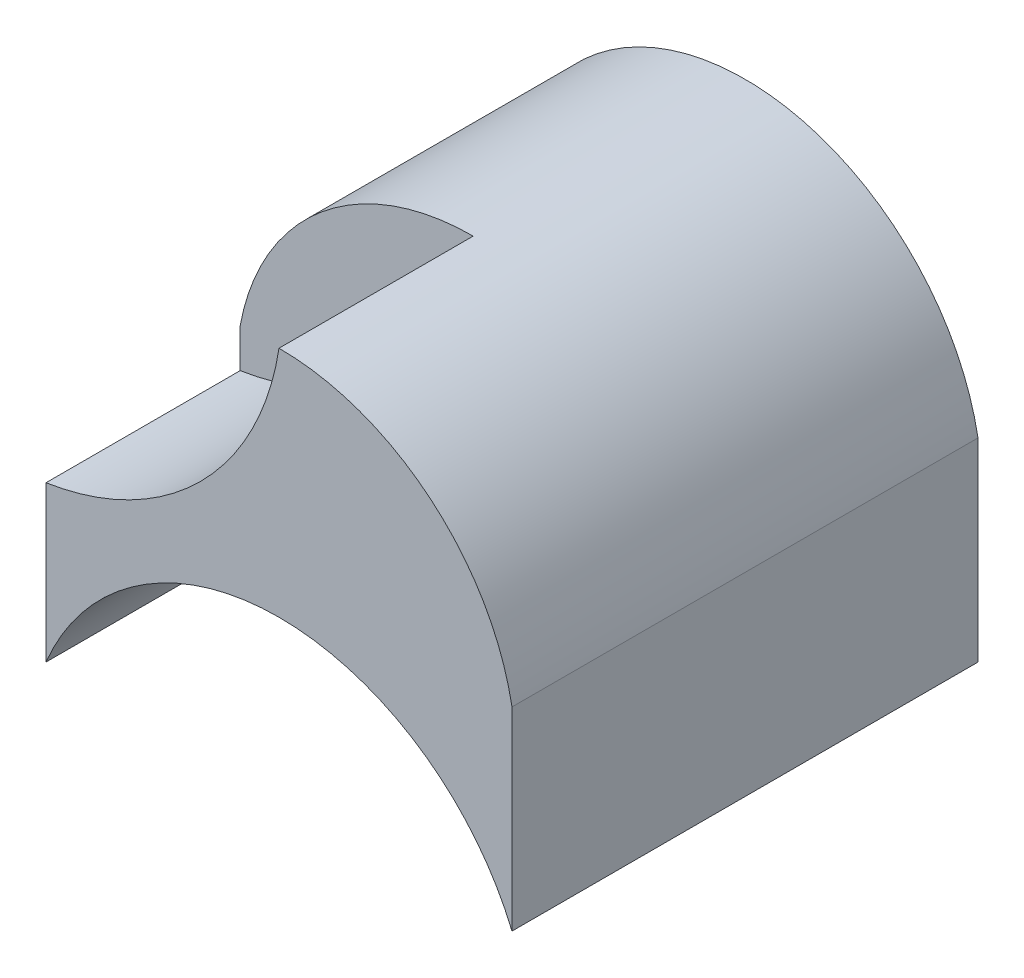
SolidWorks part; units mm, degrees
ref_plane "Front" through (0, 0, 0) normal (0, 0, 1) x (1, 0, 0)
ref_plane "Top" through (0, 0, 0) normal (0, 1, 0) x (1, 0, 0)
ref_plane "Right" through (0, 0, 0) normal (1, 0, 0) x (0, 0, -1)
sketch "Sketch1" plane through (0, 0, 0) normal (0, 1, 0) x (1, 0, 0)
  line L1 (-3, -3) -> (3, -3)
  line L2 (-3, -3) -> (-3, 3)
  line L3 (-3, 3) -> (3, 3)
  line L4 (3, -3) -> (3, 3)
  line L5 (-3, -3) -> (3, 3) construction
  line L6 (-3, 3) -> (3, -3) construction
  point P0 (0, 0)
  dimension "D1" = 6
  dimension "D2" = 6
extrude "Boss-Extrude1" add sketch "Sketch1" along normal blind 5
sketch "Sketch5" plane through (0, 0, 3) normal (0, 0, 1) x (1, 0, 0)
  line L0 (-3, 5) -> (-3, 0) construction
  line L1 (3, 5) -> (3, 0) construction
  line L6 (-3, 0) -> (3, 0)
  line L7 (3, 0) -> (3, 5)
  line L8 (3, 5) -> (-3, 5)
  line L9 (-3, 5) -> (-3, 0)
  line L10 (-3, 0) -> (3, 0)
  line L11 (3, 0) -> (3, 5)
  line L12 (3, 5) -> (-3, 5)
  line L13 (-3, 5) -> (-3, 0)
  arc A0 (-3, 0) -> (3, 0) centre (0, -1.25) cw
  arc A1 (-3, 2.5) -> (3, 2.5) centre (0, 1.95) cw
  point P8 (0, 2)
  point P14 (0, 5)
  line M5 (-3, 0) -> (3, 0)
  line M7 (3, 5) -> (-3, 5)
  line M8 (-3, 5) -> (-3, 0)
  dimension "D1" = 2
  dimension "D2" = 5
  dimension "D3" = 0
extrude "Cut-Extrude4" cut sketch "Sketch5" against normal blind 12.5 contours A1 L12 M8 | A1 L11 M7 | A0 M5
sketch "Sketch6" plane through (0, 0, 3) normal (0, 0, 1) x (1, 0, 0)
  line L0 (-3, 2.5) -> (-3, 0) construction
  line L3 (3, 0) -> (3, 2.5)
  line L4 (-3, 2.5) -> (-3, 0)
  line L5 (3, 0) -> (3, 2.5)
  line L6 (-3, 2.5) -> (-3, 0)
  arc A0 (-3, 2) -> (0, 5) centre (-3.55, 5.55) ccw
  arc A1 (3, 2.5) -> (-3, 2.5) centre (0, 1.95) ccw construction
  arc A4 (3, 2.5) -> (-3, 2.5) centre (0, 1.95) ccw
  arc A5 (3, 0) -> (-3, 0) centre (0, -1.25) ccw
  arc A6 (3, 2.5) -> (-3, 2.5) centre (0, 1.95) ccw
  arc A7 (3, 0) -> (-3, 0) centre (0, -1.25) ccw
  arc M6 (3, 2.5) -> (-3, 2.5) centre (0, 1.95) ccw
  line M7 (-3, 2.5) -> (-3, 0)
  dimension "D1" = 2
  dimension "D2" = 0
extrude "Cut-Extrude5" cut sketch "Sketch6" against normal blind 2.5 contours A0 M7 M6
